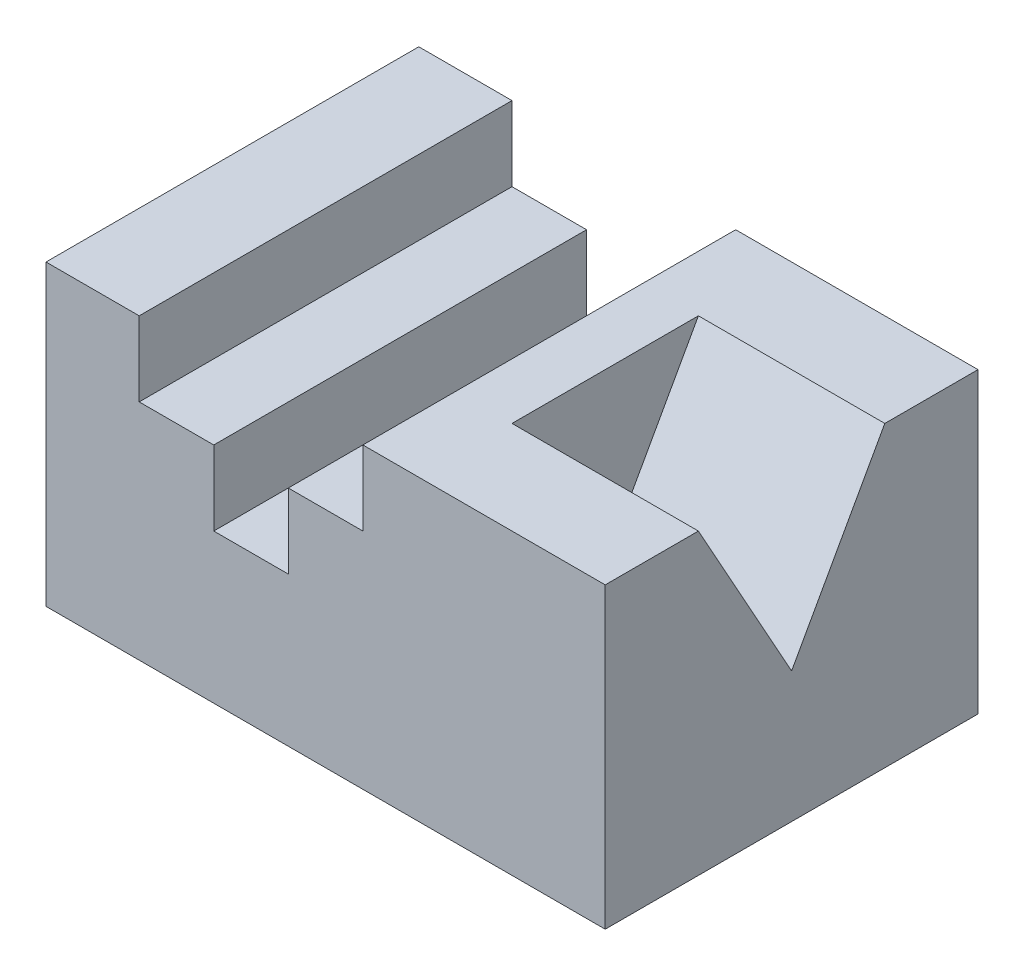
SolidWorks part; units mm, degrees
ref_plane "Front Plane" through (0, 0, 0) normal (0, 0, 1) x (1, 0, 0)
ref_plane "Top Plane" through (0, 0, 0) normal (0, 1, 0) x (1, 0, 0)
ref_plane "Right Plane" through (0, 0, 0) normal (1, 0, 0) x (0, 0, -1)
sketch "Sketch1" plane through (0, 0, 0) normal (0, 0, 1) x (1, 0, 0)
  line L1 (-71.6202, 35.0161) -> (78.3798, 35.0161)
  line L2 (-71.6202, 35.0161) -> (-71.6202, -44.9839)
  line L3 (-71.6202, -44.9839) -> (78.3798, -44.9839)
  line L4 (78.3798, 35.0161) -> (78.3798, -44.9839)
  dimension "D1" = 150
  dimension "D2" = 80
extrude "Boss-Extrude1" add sketch "Sketch1" against normal blind 100
sketch "Sketch2" plane through (0, 0, 0) normal (0, 0, 1) x (1, 0, 0)
  line L0 (78.3798, 35.0161) -> (-71.6202, 35.0161) construction
  line L1 (-46.6202, 35.0161) -> (13.3798, 35.0161)
  line L2 (-46.6202, 35.0161) -> (-46.6202, 15.0161)
  line L3 (-46.6202, 15.0161) -> (13.3798, 15.0161)
  line L4 (13.3798, 35.0161) -> (13.3798, 15.0161)
  line L5 (-71.6202, 35.0161) -> (-71.6202, -44.9839) construction
  dimension "D1" = 25
  dimension "D2" = 60
  dimension "D3" = 20
extrude "Cut-Extrude1" cut sketch "Sketch2" against normal blind 100
sketch "Sketch3" plane through (0, 0, 0) normal (0, 0, 1) x (1, 0, 0)
  line L0 (-46.6202, 15.0161) -> (13.3798, 15.0161) construction
  line L1 (-26.6202, 15.0161) -> (-6.6202, 15.0161)
  line L2 (-26.6202, 15.0161) -> (-26.6202, -4.9839)
  line L3 (-26.6202, -4.9839) -> (-6.6202, -4.9839)
  line L4 (-6.6202, 15.0161) -> (-6.6202, -4.9839)
  dimension "D1" = 20
  dimension "D2" = 20
  dimension "D3" = 20
extrude "Cut-Extrude2" cut sketch "Sketch3" against normal blind 100
sketch "Sketch4" plane through (78.3798, 0, 0) normal (1, 0, 0) x (0, 0, -1)
  line L0 (25, 35.0161) -> (50, -9.9839)
  line L1 (100, 35.0161) -> (0, 35.0161) construction
  line L2 (50, -9.9839) -> (75, 35.0161)
  line L3 (0, -44.9839) -> (0, 35.0161) construction
  dimension "D1" = 50
  dimension "D2" = 25
  dimension "D3" = 25
  dimension "D4" = 45
extrude "Cut-Extrude3" cut sketch "Sketch4" against normal blind 50 and the other way through all
